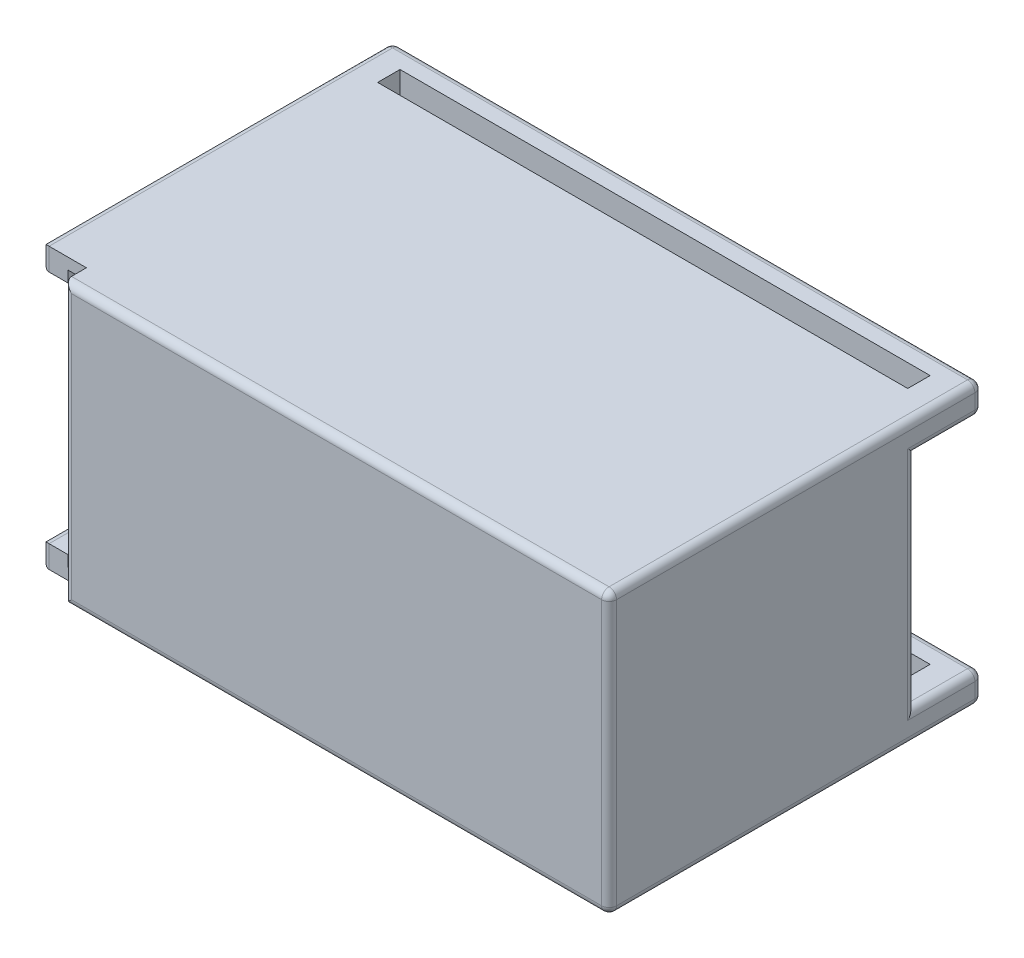
SolidWorks part; units mm, degrees
ref_plane "Piano frontale" through (0, 0, 0) normal (0, 0, 1) x (1, 0, 0)
ref_plane "Piano superiore" through (0, 0, 0) normal (0, 1, 0) x (1, 0, 0)
ref_plane "Piano destro" through (0, 0, 0) normal (1, 0, 0) x (0, 0, -1)
sketch "Sketch1" plane through (0, 0, 0) normal (0, 0, 1) x (1, 0, 0)
  line L0 (0, 37.5) -> (79, 0) construction
  line L1 (0, 0) -> (79, 0)
  line L2 (0, 0) -> (0, 37.5)
  line L3 (0, 37.5) -> (79, 37.5)
  line L4 (79, 0) -> (79, 37.5)
  line L5 (32, 23.75) -> (47, 23.75) construction
  line L6 (32, 23.75) -> (32, 13.75) construction
  line L7 (32, 13.75) -> (47, 13.75) construction
  line L8 (47, 23.75) -> (47, 13.75) construction
  line L9 (32, 13.75) -> (47, 23.75) construction
  line L10 (39.5, 18.75) -> (47, 18.75) construction
  circle A0 centre (47, 23.75) radius 2
  circle A1 centre (32, 23.75) radius 2
  circle A2 centre (32, 13.75) radius 2
  circle A3 centre (47, 13.75) radius 2
  point P9 (39.5, 18.75)
  point P10 (39.5, 18.75)
  dimension "D5" = 4
  dimension "D1" = 79
  dimension "D2" = 37.5
  dimension "D3" = 10
  dimension "D4" = 15
extrude "Body" add sketch "Sketch1" along normal blind 5
sketch "Sketch2" plane through (0, 0, 0) normal (0, 0, -1) x (-1, 0, 0)
  line L0 (0, 37.5) -> (0, 0) construction
  line L1 (-79, 37.5) -> (0, 37.5)
  line L2 (-79, 37.5) -> (-79, 33.5)
  line L3 (-79, 33.5) -> (0, 33.5)
  line L4 (0, 37.5) -> (0, 33.5)
  line L6 (-79, 0) -> (0, 0)
  line L7 (-79, 0) -> (-79, 4)
  line L8 (-79, 4) -> (0, 4)
  line L9 (0, 0) -> (0, 4)
  dimension "D1" = 4
  dimension "D2" = 4
extrude "Leg1" add sketch "Sketch2" along normal blind 3
sketch "Sketch3" plane through (0, 0, -3) normal (0, 0, -1) x (-1, 0, 0)
  line L0 (-79, 33.5) -> (0, 33.5) construction
  line L1 (-79, 37.5) -> (-75, 37.5)
  line L2 (-79, 37.5) -> (-79, 33.5)
  line L3 (-79, 33.5) -> (-75, 33.5)
  line L4 (-75, 37.5) -> (-75, 33.5)
  line L5 (-39.5, 37.5) -> (-39.5, 0) construction
  line L6 (0, 37.5) -> (-79, 37.5) construction
  line L7 (-79, 0) -> (0, 0) construction
  line L8 (-39.5, 18.75) -> (0, 18.75) construction
  line L9 (0, 33.5) -> (0, 4) construction
  line L10 (-39.5, 18.75) -> (-79, 18.75) construction
  line L11 (-79, 4) -> (-79, 33.5) construction
  line L12 (0, 33.5) -> (-4, 33.5)
  line L13 (-4, 37.5) -> (-4, 33.5)
  line L14 (0, 37.5) -> (-4, 37.5)
  line L15 (0, 37.5) -> (0, 33.5)
  line L16 (0, 0) -> (0, 4)
  line L17 (0, 0) -> (-4, 0)
  line L18 (-4, 0) -> (-4, 4)
  line L19 (0, 4) -> (-4, 4)
  line L20 (-79, 4) -> (-75, 4)
  line L21 (-75, 0) -> (-75, 4)
  line L22 (-79, 0) -> (-75, 0)
  line L23 (-79, 0) -> (-79, 4)
  dimension "D1" = 4
  dimension "D2" = 71
extrude "Leg2" add sketch "Sketch3" along normal blind 3
sketch "Sketch4" plane through (0, 0, -6) normal (0, 0, -1) x (-1, 0, 0)
  line L1 (-79, 37.5) -> (0, 37.5)
  line L2 (-79, 37.5) -> (-79, 33.5)
  line L3 (-79, 33.5) -> (0, 33.5)
  line L4 (0, 37.5) -> (0, 33.5)
  line L5 (-79, 4) -> (0, 4)
  line L6 (-79, 4) -> (-79, 0)
  line L7 (-79, 0) -> (0, 0)
  line L8 (0, 4) -> (0, 0)
extrude "Leg3" add sketch "Sketch4" along normal blind 3
sketch "Sketch5" plane through (0, 0, 5) normal (0, 0, 1) x (1, 0, 0)
  line L0 (79, 0) -> (79, 37.5) construction
  line L1 (0, 37.5) -> (79, 37.5)
  line L2 (0, 37.5) -> (0, 34.5)
  line L3 (3, 34.5) -> (76, 34.5)
  line L4 (79, 37.5) -> (79, 34.5)
  line L18 (79, 37.5) -> (0, 37.5) construction
  line L21 (79, 29.6854) -> (79, 34.5)
  line L22 (0, 37.5) -> (0, 0) construction
  line L23 (0, 18.75) -> (79, 18.75) construction
  line L26 (3, 3) -> (76, 3)
  line L30 (0, 0) -> (0, 3)
  line L31 (0, 0) -> (79, 0)
  line L32 (79, 0) -> (79, 3)
  line L33 (79, 7.8146) -> (79, 3)
  line L34 (79, 29.6854) -> (79, 7.8146)
  line L35 (0, 34.5) -> (3, 34.5)
  line L36 (0, 3) -> (3, 3)
  line L37 (76, 34.5) -> (76, 3)
  dimension "D1" = 3
  dimension "D2" = 3
extrude "Walls" add sketch "Sketch5" along normal blind 33
sketch "Sketch6" plane through (0, 0, 38) normal (0, 0, 1) x (1, 0, 0)
  line L0 (79, 37.5) -> (0, 37.5) construction
  line L1 (5.5, 36) -> (3.5, 36)
  line L2 (5.5, 36) -> (5.5, 1.5)
  line L3 (5.5, 1.5) -> (3.5, 1.5)
  line L4 (3.5, 36) -> (3.5, 1.5)
  line L7 (0, 37.5) -> (0, 34.5) construction
  line L8 (76, 3) -> (0, 3) construction
  dimension "D1" = 2
  dimension "D2" = 1.5
  dimension "D3" = 1.5
  dimension "D4" = 34.5
  dimension "D5" = 3.5
extrude "Cut-Extrude1" cut sketch "Sketch6" against normal blind 17
sketch "Sketch7" plane through (0, 0, 38) normal (0, 0, 1) x (1, 0, 0)
  line L0 (79, 37.5) -> (0, 37.5) construction
  line L1 (6, 37.5) -> (79, 37.5)
  line L2 (6, 37.5) -> (6, 0)
  line L3 (6, 0) -> (79, 0)
  line L4 (79, 37.5) -> (79, 0)
  line L5 (5.5, 34.5) -> (5.5, 36) construction
  dimension "D1" = 0.5
extrude "Boss-Extrude1" add sketch "Sketch7" along normal blind 3
fillet "Fillet1" radius 1 1 edges at (39.5, 37.5, -9)
fillet "Fillet2" radius 1 1 edges at (39.5, 33.5, -9)
fillet "Fillet3" radius 1 1 edges at (39.5, 0, -9)
fillet "Fillet4" radius 1 1 edges at (39.5, 4, -9)
fillet "Fillet6" radius 1 30 edges at (0, 18.75, 0) (0, 33.5, -4) (0, 33.7929, -8.7071) (0, 35.5, -9) (0, 37.2071, -8.7071) (0, 37.5, 15) (0, 1.5, 38) (0, 34.5, 21.5) (0, 18.75, 5) (0, 3, 21.5) (0, 0, 15) (0, 0.2929, -8.7071) (0, 2, -9) (0, 3.7071, -8.7071) (0, 4, -4) (79, 0.2929, -8.7071) (79, 0, 16.5) (79, 18.75, 41) (79, 37.5, 16.5) (79, 37.2071, -8.7071) (79, 35.5, -9) (79, 33.7929, -8.7071) (79, 33.5, -4) (79, 18.75, 0) (79, 4, -4) (79, 3.7071, -8.7071) (79, 2, -9) (42.5, 37.5, 41) (42.5, 0, 41) (6, 18.75, 41)
ref_plane "Plane1" through (3.5, 34.5, 21) normal (-1, 0, 0) x (0, 0, 1)
sketch "Sketch8" plane through (76, 0, 0) normal (-1, 0, 0) x (0, 0, 1)
  line L0 (38, 34.5) -> (5, 34.5) construction
  line L1 (27.5, 34.5) -> (32.5, 34.5)
  line L2 (27.5, 34.5) -> (27.5, 3)
  line L3 (27.5, 3) -> (32.5, 3)
  line L4 (32.5, 34.5) -> (32.5, 3)
  line L5 (38, 3) -> (5, 3) construction
  line L6 (5, 34.5) -> (5, 3) construction
  dimension "D1" = 22.5
  dimension "D2" = 5
extrude "Boss-Extrude2" add sketch "Sketch8" along normal blind 16
